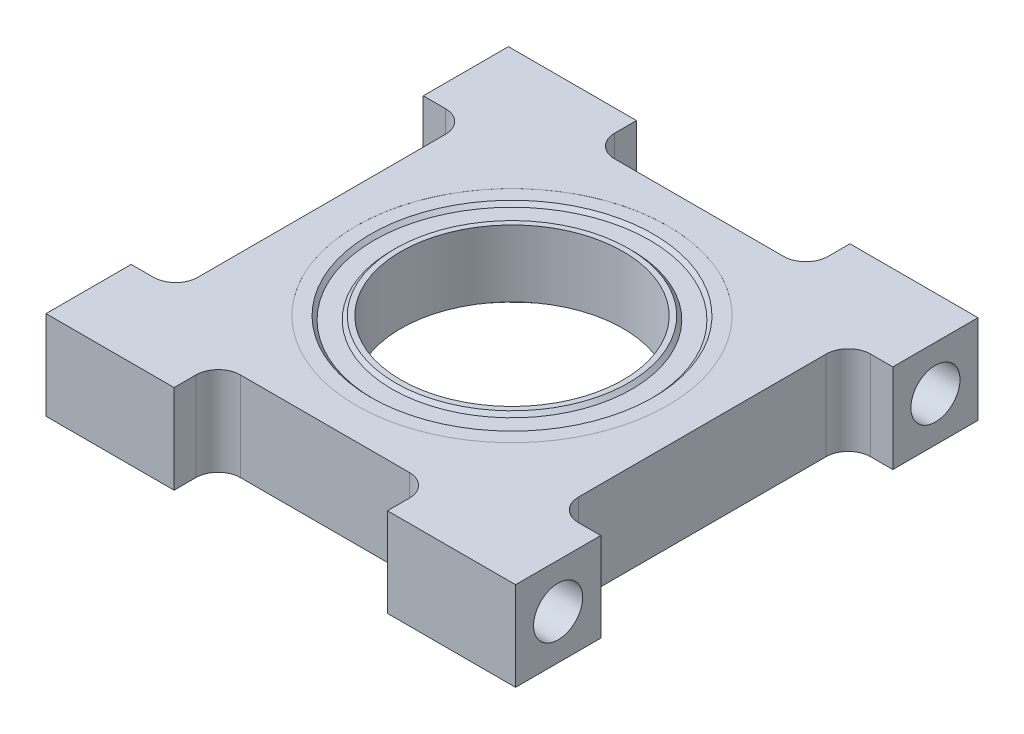
SolidWorks part; units mm, degrees
material "6061 Alloy"
ref_plane "Front Plane" through (0, 0, 0) normal (0, 0, 1) x (1, 0, 0)
ref_plane "Top Plane" through (0, 0, 0) normal (0, 1, 0) x (1, 0, 0)
ref_plane "Right Plane" through (0, 0, 0) normal (1, 0, 0) x (0, 0, -1)
sketch "Sketch1" plane through (0, 0, 0) normal (0, 1, 0) x (1, 0, 0)
  line L0 (-16.764, 0) -> (16.764, 0) construction
  line L1 (-16.764, -16.51) -> (-7.62, -16.51)
  line L2 (-16.764, -16.51) -> (-16.764, -10.4267)
  line L3 (-16.764, 16.51) -> (-7.62, 16.51)
  line L4 (16.764, -16.51) -> (16.764, -10.4267)
  line L5 (-16.764, -16.51) -> (16.764, 16.51) construction
  line L6 (-16.764, 16.51) -> (16.764, -16.51) construction
  line L7 (0, 16.51) -> (0, -16.51) construction
  line L8 (-7.62, -16.51) -> (-7.62, -14.9479)
  line L9 (-6.0325, -13.3604) -> (6.0325, -13.3604)
  line L10 (7.62, -14.9479) -> (7.62, -16.51)
  line L11 (7.62, -16.51) -> (16.764, -16.51)
  line L12 (7.62, 14.9479) -> (7.62, 16.51)
  line L13 (-6.0325, 13.3604) -> (6.0325, 13.3604)
  line L14 (-7.62, 16.51) -> (-7.62, 14.9479)
  line L15 (7.62, 16.51) -> (16.764, 16.51)
  line L16 (-16.764, 10.4267) -> (-15.1765, 10.4267)
  line L17 (-13.589, 8.8392) -> (-13.589, -8.8392)
  line L18 (-15.1765, -10.4267) -> (-16.764, -10.4267)
  line L19 (-16.764, 10.4267) -> (-16.764, 16.51)
  line L20 (15.1765, -10.4267) -> (16.764, -10.4267)
  line L21 (13.589, 8.8392) -> (13.589, -8.8392)
  line L22 (16.764, 10.4267) -> (15.1765, 10.4267)
  line L23 (16.764, 10.4267) -> (16.764, 16.51)
  arc A0 (6.0325, -13.3604) -> (7.62, -14.9479) centre (6.0325, -14.9479) cw
  arc A1 (-7.62, -14.9479) -> (-6.0325, -13.3604) centre (-6.0325, -14.9479) cw
  arc A2 (-7.62, 14.9479) -> (-6.0325, 13.3604) centre (-6.0325, 14.9479) ccw
  arc A3 (6.0325, 13.3604) -> (7.62, 14.9479) centre (6.0325, 14.9479) ccw
  arc A4 (-13.589, -8.8392) -> (-15.1765, -10.4267) centre (-15.1765, -8.8392) cw
  arc A5 (-15.1765, 10.4267) -> (-13.589, 8.8392) centre (-15.1765, 8.8392) cw
  arc A6 (15.1765, 10.4267) -> (13.589, 8.8392) centre (15.1765, 8.8392) ccw
  arc A7 (13.589, -8.8392) -> (15.1765, -10.4267) centre (15.1765, -8.8392) ccw
  circle A8 centre (0, 0) radius 10.16
  point P0 (0, 0)
  dimension "D6" = 1.5875
  dimension "D10" = 1.5875
  dimension "D11" = 20.32
  dimension "D1" = 33.02
  dimension "D2" = 33.528
  dimension "D3" = 15.24
  dimension "D4" = 7.62
  dimension "D5" = 3.1496
  dimension "D7" = 20.8534
  dimension "D8" = 10.4267
  dimension "D9" = 3.175
extrude "Boss-Extrude1" add sketch "Sketch1" along normal blind 6.35
sketch "Sketch2" plane through (0, 6.35, 0) normal (0, 1, 0) x (1, 0, 0)
  circle A0 centre (0, 0) radius 11.1125
  dimension "D1" = 22.225
extrude "Cut-Extrude1" cut sketch "Sketch2" against normal blind 4.7625
ref_plane "Plane1" through (0, 1.5875, 0) normal (0, 1, 0) x (-1, 0, 0)
sketch "Sketch3" plane through (0, 1.5875, 0) normal (0, 1, 0) x (-1, 0, 0)
  circle A0 centre (0, 0) radius 11.1125
  circle A1 centre (0, 0) radius 9.8425
  dimension "D1" = 1.27
extrude "Boss-Extrude2" add sketch "Sketch3" along normal blind 4.76
chamfer "Chamfer1" distance 0.254 angle 45 2 edges at (0, 1.5875, 9.8425) (0, 6.3475, 9.8425)
sketch "Sketch4" plane through (0, 1.5875, 0) normal (0, 1, 0) x (-1, 0, 0)
  circle A0 centre (0, 0) radius 7.9375
  circle A1 centre (0, 0) radius 8.5725
  dimension "D1" = 15.875
  dimension "D2" = 0.635
extrude "Boss-Extrude3" add sketch "Sketch4" along normal blind 4.76 separate body
chamfer "Chamfer2" distance 0.254 angle 45 2 edges at (0, 1.5875, 8.5725) (0, 6.3475, 8.5725)
ref_plane "Plane2" through (0, 6.0935, 0) normal (0, 1, 0) x (-1, 0, 0)
sketch "Sketch5" plane through (0, 6.0935, 0) normal (0, 1, 0) x (-1, 0, 0)
  circle A0 centre (0, 0) radius 9.8425
  circle A1 centre (0, 0) radius 8.5725
extrude "Boss-Extrude4" add sketch "Sketch5" against normal blind 4.2545
hole_wizard "#6-32 Tapped Hole1" positions "Sketch9" profile "Sketch8" tap size "#6-32" standard "Ansi Inch"
sketch "Sketch9" plane through (-16.764, 0, 0) normal (-1, 0, 0) x (0, 0, 1)
  line L0 (-13.4704, 3.175) -> (13.4704, 3.175) construction
  line L1 (-13.4704, 3.175) -> (0, 16.6454) construction
  line L2 (13.4704, 3.175) -> (0, 16.6454) construction
  line L3 (-16.51, 0) -> (-10.4267, 0) construction
  point P0 (-13.4704, 3.175)
  point P1 (13.4704, 3.175)
  dimension "D1" = 19.05
  dimension "D2" = 19.05
  dimension "D3" = 3.175
sketch "Sketch8" plane through (-16.764, 3.175, -13.4704) normal (0, 1, 0) x (0, 0, 1)
  line L0 (0, 0) -> (0, 8.7629)
  line L1 (0, 8.7629) -> (1.3525, 7.9502)
  line L2 (1.3525, 7.9502) -> (1.3525, 7.0104)
  line L3 (1.3525, 7.0104) -> (1.7526, 7.0104)
  line L4 (1.7526, 7.0104) -> (1.7526, 0)
  line L5 (1.7526, 0) -> (0, 0)
  line L10 (0, 8.7629) -> (-1.3526, 7.9502) construction
  line L11 (0, -6.35) -> (0, 107.95) construction
  dimension "Tap Drill Dia." = 2.7051
  dimension "Tap Drill Depth" = 7.9502
  dimension "Thread Major Dia." = 3.5052
  dimension "Thread Depth" = 7.0104
  dimension "Drill Angle" = 118
mirror "Mirror1" about plane through (0, 0, 0) normal (1, 0, 0) of "#6-32 Tapped Hole1"
